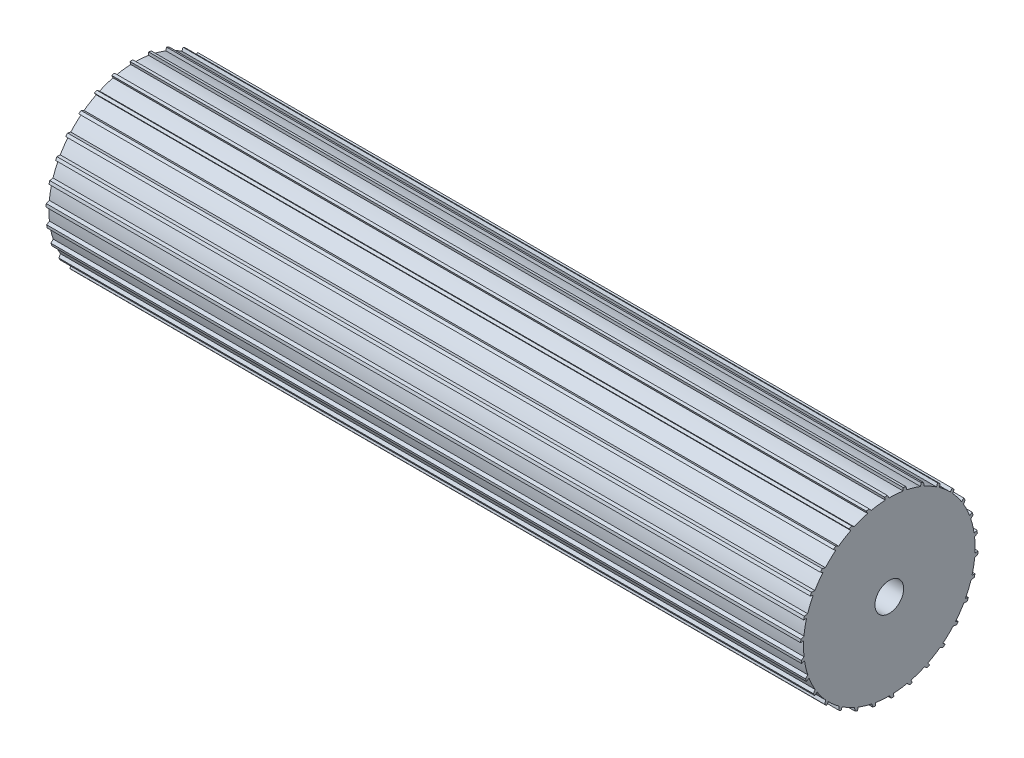
SolidWorks part; units mm, degrees
ref_plane "Ön Düzlem" through (0, 0, 0) normal (0, 0, 1) x (1, 0, 0)
ref_plane "Üst Düzlem" through (0, 0, 0) normal (0, 1, 0) x (1, 0, 0)
ref_plane "Sağ Düzlem" through (0, 0, 0) normal (1, 0, 0) x (0, 0, -1)
sketch "Çizim1" plane through (0, 0, 0) normal (0, 0, 1) x (1, 0, 0)
  line L0 (-74.6314, 0) -> (135.3686, 0)
  line L1 (135.3686, 0) -> (135.3686, -20)
  line L2 (135.3686, -20) -> (165.3686, -20)
  line L3 (165.3686, -20) -> (165.3686, -23.875)
  line L4 (165.3686, -23.875) -> (-104.6314, -23.875)
  line L5 (30.3686, 0) -> (30.3686, -46.9069) construction
  line L6 (-74.6314, 0) -> (-74.6314, -20)
  line L7 (-104.6314, -20) -> (-104.6314, -23.875)
  line L8 (-74.6314, -20) -> (-104.6314, -20)
  point P12 (30.3686, -23.875)
  dimension "D1" = 210
  dimension "D2" = 30
  dimension "D3" = 20
  dimension "D4" = 3.875
revolve "Döndür2" add sketch "Çizim1" angle 360 about L4
sketch "Çizim2" plane through (-74.6314, 0, 0) normal (-1, 0, 0) x (0, 0, 1)
  line L0 (-0.2399, -0.5771) -> (0.5103, 0.8077)
  line L1 (0.5103, 0.8077) -> (1.3098, 0.8077)
  line L2 (1.3098, 0.8077) -> (0.91, -0.7832)
  line L3 (0.91, -0.7832) -> (-0.2399, -0.5771)
  line L120 (5.6912, -1.477) -> (4.6093, -1.0363)
  line L121 (6.413, -0.004) -> (5.6912, -1.477)
  line L122 (5.6309, 0.1623) -> (6.413, -0.004)
  line L123 (4.6093, -1.0363) -> (5.6309, 0.1623)
  line L124 (10.2237, -3.1497) -> (9.257, -2.4938)
  line L125 (11.236, -1.859) -> (10.2237, -3.1497)
  line L126 (10.5055, -1.5337) -> (11.236, -1.859)
  line L127 (9.257, -2.4938) -> (10.5055, -1.5337)
  line L128 (14.3093, -5.7282) -> (13.5001, -4.8856)
  line L129 (15.5678, -4.6762) -> (14.3093, -5.7282)
  line L130 (14.9209, -4.2062) -> (15.5678, -4.6762)
  line L131 (13.5001, -4.8856) -> (14.9209, -4.2062)
  line L132 (17.7695, -9.0998) -> (17.1532, -8.1074)
  line L133 (19.2193, -8.3324) -> (17.7695, -9.0998)
  line L134 (18.6843, -7.7382) -> (19.2193, -8.3324)
  line L135 (17.1532, -8.1074) -> (18.6843, -7.7382)
  line L136 (20.4531, -13.1172) -> (20.0566, -12.0183)
  line L137 (22.0308, -12.668) -> (20.4531, -13.1172)
  line L138 (21.631, -11.9755) -> (22.0308, -12.668)
  line L139 (20.0566, -12.0183) -> (21.631, -11.9755)
  line L140 (22.2428, -17.6047) -> (22.0835, -16.4474)
  line L141 (23.8794, -17.4933) -> (22.2428, -17.6047)
  line L142 (23.6323, -16.7329) -> (23.8794, -17.4933)
  line L143 (22.0835, -16.4474) -> (23.6323, -16.7329)
  line L144 (23.0605, -22.3663) -> (23.1452, -21.2012)
  line L145 (24.6844, -22.5976) -> (23.0605, -22.3663)
  line L146 (24.6008, -21.8024) -> (24.6844, -22.5976)
  line L147 (23.1452, -21.2012) -> (24.6008, -21.8024)
  line L148 (22.8702, -27.1938) -> (23.1953, -26.0717)
  line L149 (24.4106, -27.7577) -> (22.8702, -27.1938)
  line L150 (24.4942, -26.9625) -> (24.4106, -27.7577)
  line L151 (23.1953, -26.0717) -> (24.4942, -26.9625)
  line L152 (21.6804, -31.8763) -> (22.2317, -30.8463)
  line L153 (23.0699, -32.7481) -> (21.6804, -31.8763)
  line L154 (23.317, -31.9877) -> (23.0699, -32.7481)
  line L155 (22.2317, -30.8463) -> (23.317, -31.9877)
  line L156 (19.5431, -36.209) -> (20.2965, -35.3162)
  line L157 (20.721, -37.3507) -> (19.5431, -36.209)
  line L158 (21.1207, -36.6583) -> (20.721, -37.3507)
  line L159 (20.2965, -35.3162) -> (21.1207, -36.6583)
  line L160 (16.5516, -40.0027) -> (17.4742, -39.2861)
  line L161 (17.4664, -41.3644) -> (16.5516, -40.0027)
  line L162 (18.0014, -40.7702) -> (17.4664, -41.3644)
  line L163 (17.4742, -39.2861) -> (18.0014, -40.7702)
  line L164 (12.8368, -43.0916) -> (13.8882, -42.5824)
  line L165 (13.4485, -44.6136) -> (12.8368, -43.0916)
  line L166 (14.0953, -44.1437) -> (13.4485, -44.6136)
  line L167 (13.8882, -42.5824) -> (14.0953, -44.1437)
  line L168 (8.5609, -45.3406) -> (9.6952, -45.0611)
  line L169 (8.8428, -46.9565) -> (8.5609, -45.3406)
  line L170 (9.5732, -46.6313) -> (8.8428, -46.9565)
  line L171 (9.6952, -45.0611) -> (9.5732, -46.6313)
  line L172 (3.9109, -46.6514) -> (5.0785, -46.6139)
  line L173 (3.8506, -48.2907) -> (3.9109, -46.6514)
  line L174 (4.6327, -48.1244) -> (3.8506, -48.2907)
  line L175 (5.0785, -46.6139) -> (4.6327, -48.1244)
  line L176 (-0.91, -46.9668) -> (0.2399, -47.1729)
  line L177 (-1.3098, -48.5577) -> (-0.91, -46.9668)
  line L178 (-0.5103, -48.5577) -> (-1.3098, -48.5577)
  line L179 (0.2399, -47.1729) -> (-0.5103, -48.5577)
  line L180 (-5.6912, -46.273) -> (-4.6093, -46.7137)
  line L181 (-6.413, -47.746) -> (-5.6912, -46.273)
  line L182 (-5.6309, -47.9123) -> (-6.413, -47.746)
  line L183 (-4.6093, -46.7137) -> (-5.6309, -47.9123)
  line L184 (-10.2237, -44.6003) -> (-9.257, -45.2562)
  line L185 (-11.236, -45.891) -> (-10.2237, -44.6003)
  line L186 (-10.5055, -46.2163) -> (-11.236, -45.891)
  line L187 (-9.257, -45.2562) -> (-10.5055, -46.2163)
  line L188 (-14.3093, -42.0218) -> (-13.5001, -42.8644)
  line L189 (-15.5678, -43.0738) -> (-14.3093, -42.0218)
  line L190 (-14.9209, -43.5438) -> (-15.5678, -43.0738)
  line L191 (-13.5001, -42.8644) -> (-14.9209, -43.5438)
  line L192 (-17.7695, -38.6502) -> (-17.1532, -39.6426)
  line L193 (-19.2193, -39.4176) -> (-17.7695, -38.6502)
  line L194 (-18.6843, -40.0118) -> (-19.2193, -39.4176)
  line L195 (-17.1532, -39.6426) -> (-18.6843, -40.0118)
  line L196 (-20.4531, -34.6328) -> (-20.0566, -35.7317)
  line L197 (-22.0308, -35.082) -> (-20.4531, -34.6328)
  line L198 (-21.631, -35.7745) -> (-22.0308, -35.082)
  line L199 (-20.0566, -35.7317) -> (-21.631, -35.7745)
  line L200 (-22.2428, -30.1453) -> (-22.0835, -31.3026)
  line L201 (-23.8794, -30.2567) -> (-22.2428, -30.1453)
  line L202 (-23.6323, -31.0171) -> (-23.8794, -30.2567)
  line L203 (-22.0835, -31.3026) -> (-23.6323, -31.0171)
  line L204 (-23.0605, -25.3837) -> (-23.1452, -26.5488)
  line L205 (-24.6844, -25.1524) -> (-23.0605, -25.3837)
  line L206 (-24.6008, -25.9476) -> (-24.6844, -25.1524)
  line L207 (-23.1452, -26.5488) -> (-24.6008, -25.9476)
  line L208 (-22.8702, -20.5562) -> (-23.1953, -21.6783)
  line L209 (-24.4106, -19.9923) -> (-22.8702, -20.5562)
  line L210 (-24.4942, -20.7875) -> (-24.4106, -19.9923)
  line L211 (-23.1953, -21.6783) -> (-24.4942, -20.7875)
  line L212 (-21.6804, -15.8737) -> (-22.2317, -16.9037)
  line L213 (-23.0699, -15.0019) -> (-21.6804, -15.8737)
  line L214 (-23.317, -15.7623) -> (-23.0699, -15.0019)
  line L215 (-22.2317, -16.9037) -> (-23.317, -15.7623)
  line L216 (-19.5431, -11.541) -> (-20.2965, -12.4338)
  line L217 (-20.721, -10.3993) -> (-19.5431, -11.541)
  line L218 (-21.1207, -11.0917) -> (-20.721, -10.3993)
  line L219 (-20.2965, -12.4338) -> (-21.1207, -11.0917)
  line L220 (-16.5516, -7.7473) -> (-17.4742, -8.4639)
  line L221 (-17.4664, -6.3856) -> (-16.5516, -7.7473)
  line L222 (-18.0014, -6.9798) -> (-17.4664, -6.3856)
  line L223 (-17.4742, -8.4639) -> (-18.0014, -6.9798)
  line L224 (-12.8368, -4.6584) -> (-13.8882, -5.1676)
  line L225 (-13.4485, -3.1364) -> (-12.8368, -4.6584)
  line L226 (-14.0953, -3.6063) -> (-13.4485, -3.1364)
  line L227 (-13.8882, -5.1676) -> (-14.0953, -3.6063)
  line L228 (-8.5609, -2.4094) -> (-9.6952, -2.6889)
  line L229 (-8.8428, -0.7935) -> (-8.5609, -2.4094)
  line L230 (-9.5732, -1.1187) -> (-8.8428, -0.7935)
  line L231 (-9.6952, -2.6889) -> (-9.5732, -1.1187)
  line L232 (-3.9109, -1.0986) -> (-5.0785, -1.1361)
  line L233 (-3.8506, 0.5407) -> (-3.9109, -1.0986)
  line L234 (-4.6327, 0.3744) -> (-3.8506, 0.5407)
  line L235 (-5.0785, -1.1361) -> (-4.6327, 0.3744)
  point P123 (0, -23.875)
  point P124 (0, -26)
extrude "Yükseklik-Ekstrüzyon1" add sketch "Çizim2" against normal up to surface (210 mm away) up to face at (135.3686, 0, 0)
sketch "Çizim5" plane through (0, 0, 0) normal (0, 0, 1) x (1, 0, 0)
  line L0 (-74.6314, -20) -> (-74.6314, -27.75) construction
  circle A0 centre (-101.6314, -23.9587) radius 1.5
  dimension "D1" = 3
  dimension "D2" = 27
extrude "Kes-Ekstrüzyon1" cut sketch "Çizim5" against normal blind 10 and the other way blind 35
sketch "Çizim6" plane through (0, 0, 0) normal (0, 0, 1) x (1, 0, 0)
  line L0 (135.3686, -27.75) -> (135.3686, -20) construction
  circle A0 centre (162.3686, -23.875) radius 1.5
  dimension "D1" = 3
  dimension "D2" = 27
extrude "Kes-Ekstrüzyon2" cut sketch "Çizim6" against normal blind 10 and the other way blind 67
sketch "Çizim7" plane through (165.3686, 0, 0) normal (1, 0, 0) x (0, 0, -1)
  circle A1 centre (0, -23.875) radius 3.995
  dimension "D1" = 7.99
extrude "Kes-Ekstrüzyon3" cut sketch "Çizim7" against normal blind 310
